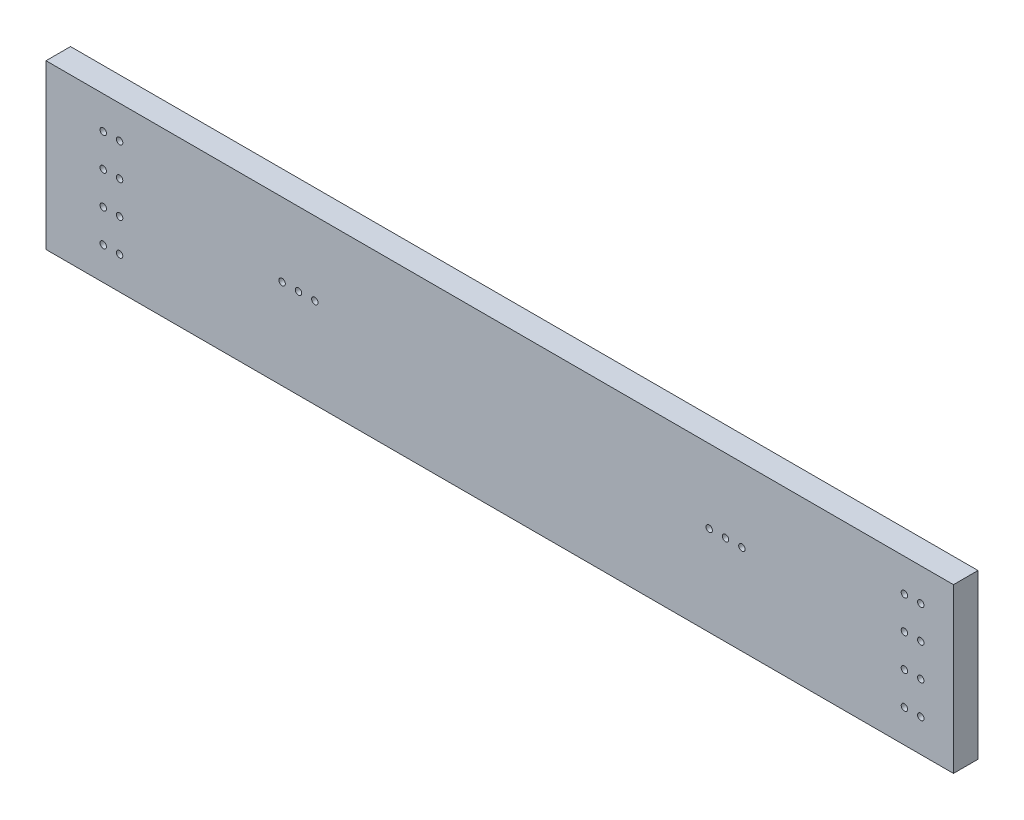
SolidWorks part; units mm, degrees
material "Pine"
ref_plane "Front Plane" through (0, 0, 0) normal (0, 0, 1) x (1, 0, 0)
ref_plane "Top Plane" through (0, 0, 0) normal (0, 1, 0) x (1, 0, 0)
ref_plane "Right Plane" through (0, 0, 0) normal (1, 0, 0) x (0, 0, -1)
sketch "robot, section, top of tube" plane through (0, 0, 0) normal (0, 1, 0) x (1, 0, 0)
  line L1 (-330.2, 0) -> (330.2, 0)
  line L2 (-330.2, 0) -> (-330.2, 660.4)
  line L3 (-330.2, 660.4) -> (330.2, 660.4)
  line L4 (330.2, 0) -> (330.2, 660.4)
  line L6 (146.05, 0) -> (146.05, 45.2974)
  line L7 (-146.05, 0) -> (-146.05, 45.2974)
  line L8 (0, 0) -> (0, 660.4) construction
  dimension "D1" = 660.4
  dimension "D3" = 184.15
sketch "robot approx side" plane through (0, 0, 0) normal (0, 0, 1) x (1, 0, 0)
  line L0 (-146.812, 0) -> (-146.812, 25.4)
  line L1 (-330.2, 0) -> (330.2, 0) construction
  line L2 (-146.812, 2.6416) -> (-121.9604, 2.6416)
  line L4 (0, 0) -> (0, 48.6273) construction
  line L5 (146.812, 2.6416) -> (121.9604, 2.6416)
  line L6 (146.812, 0) -> (146.812, 25.4)
  dimension "D1" = 2.6416
  dimension "D2" = 25.4
  dimension "D3" = 183.388
ref_plane "floor" through (0, -93.726, 0) normal (0, 1, 0) x (1, 0, 0)
ref_plane "bottom" through (0, -57.15, 0) normal (0, 1, 0) x (1, 0, 0)
ref_plane "top" through (0, 69.85, 0) normal (0, 1, 0) x (1, 0, 0)
sketch "Sketch4" plane through (0, 0, 0) normal (0, 1, 0) x (1, 0, 0)
  line L0 (-330.2, 0) -> (330.2, 0) construction
  line L1 (342.9, -12.7) -> (-361.95, -12.7)
  line L2 (342.9, -12.7) -> (342.9, -31.75)
  line L3 (342.9, -31.75) -> (-361.95, -31.75)
  line L4 (-361.95, -12.7) -> (-361.95, -31.75)
  line L5 (330.2, 0) -> (330.2, 660.4) construction
  line L6 (-330.2, 0) -> (-330.2, 660.4) construction
  dimension "D1" = 19.05
  dimension "D2" = 12.7
  dimension "D3" = 12.7
  dimension "D4" = 31.75
extrude "Boss-Extrude1" add sketch "Sketch4" along normal up to surface (127 mm away) from surface at -57.15 up to plane "top" starting at plane "bottom"
sketch "Sketch5" plane through (0, 0, 31.75) normal (0, 0, 1) x (1, 0, 0)
  line L0 (-9.525, 69.85) -> (-9.525, -57.15) construction
  line L1 (146.812, 0) -> (146.812, 25.4) construction
  line L2 (-361.95, 69.85) -> (-361.95, -57.15) construction
  line L4 (-361.95, 69.85) -> (342.9, 69.85) construction
  line L5 (-361.95, -57.15) -> (342.9, -57.15) construction
  line L6 (-361.95, 12.7) -> (342.9, 12.7) construction
  line L7 (342.9, 69.85) -> (342.9, -57.15) construction
  line L8 (-146.812, 0) -> (-146.812, 25.4) construction
  circle A0 centre (-317.5, 44.45) radius 2.4955
  circle A1 centre (-304.8, 44.45) radius 2.4955
  circle A2 centre (-317.5, 19.05) radius 2.4955
  circle A3 centre (-304.8, 19.05) radius 2.4955
  circle A4 centre (-317.5, -6.35) radius 2.4955
  circle A5 centre (-304.8, -6.35) radius 2.4955
  circle A6 centre (-317.5, -31.75) radius 2.4955
  circle A7 centre (-304.8, -31.75) radius 2.4955
  circle A14 centre (304.8, 44.45) radius 2.4955
  circle A15 centre (317.5, 44.45) radius 2.4955
  circle A16 centre (-178.562, 12.7) radius 2.4892
  circle A17 centre (-165.862, 12.7) radius 2.4892
  circle A18 centre (-153.162, 12.7) radius 2.4892
  circle A19 centre (153.162, 12.7) radius 2.4892
  circle A20 centre (165.862, 12.7) radius 2.4892
  circle A21 centre (178.562, 12.7) radius 2.4892
  circle A22 centre (317.5, 19.05) radius 2.4955
  circle A23 centre (304.8, 19.05) radius 2.4955
  circle A24 centre (317.5, -6.35) radius 2.4955
  circle A25 centre (304.8, -6.35) radius 2.4955
  circle A26 centre (317.5, -31.75) radius 2.4955
  circle A27 centre (304.8, -31.75) radius 2.4955
  point P30 (-146.812, 12.7)
  dimension "D3" = 4.9911
  dimension "D1" = 4.9784
  dimension "D9" = 12.7
  dimension "D10" = 6.35
  dimension "D11" = 6.35
  dimension "D12" = 12.7
  dimension "D13" = 12.7
  dimension "D16" = 25.4
  dimension "D2" = 12.7
  dimension "D4" = 25.4
  dimension "D5" = 44.45
  dimension "D7" = 25.4
  dimension "D8" = 12.7
  dimension "D14" = 25.4
  dimension "D15" = 12.7
  dimension "D18" = 25.4
  dimension "D6" = 4
  dimension "D17" = 4
extrude "Cut-Extrude1" cut sketch "Sketch5" against normal through all
equation "\"D3@Sketch4\"=\"D2@Sketch4\""
equation "\"D4@Sketch4\"=.75+\"D2@Sketch4\""
